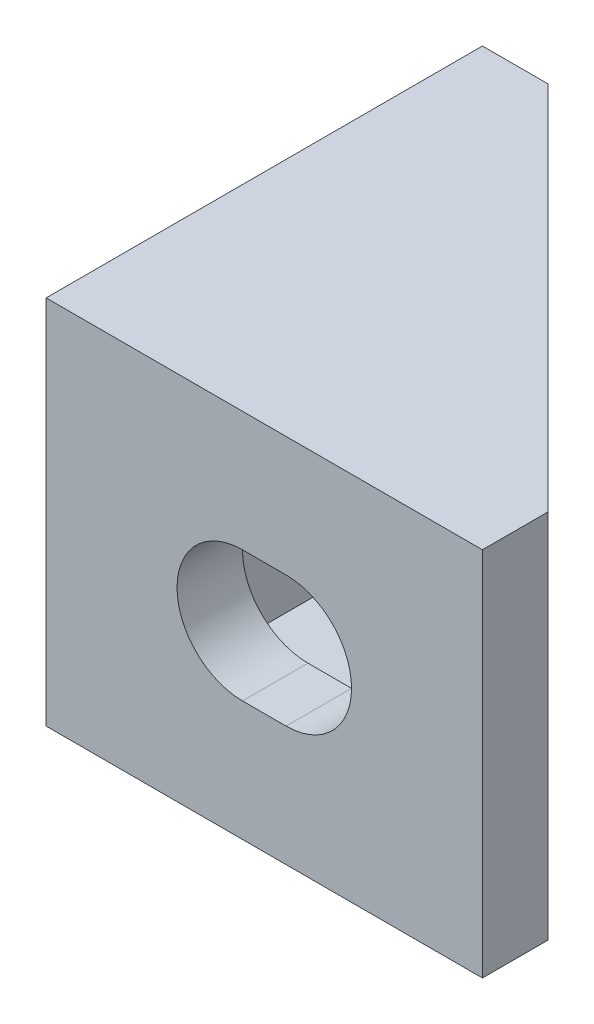
SolidWorks part; units mm, degrees
ref_plane "Front Plane" through (0, 0, 0) normal (0, 0, 1) x (1, 0, 0)
ref_plane "Top Plane" through (0, 0, 0) normal (0, 1, 0) x (1, 0, 0)
ref_plane "Right Plane" through (0, 0, 0) normal (1, 0, 0) x (0, 0, -1)
sketch "Sketch1" plane through (0, 0, 0) normal (0, 1, 0) x (1, 0, 0)
  line L0 (0, 0) -> (20, 0)
  line L1 (20, 0) -> (20, 3)
  line L2 (20, 3) -> (3, 20)
  line L3 (3, 20) -> (0, 20)
  line L4 (0, 20) -> (0, 0)
  dimension "D1" = 20
  dimension "D2" = 20
  dimension "D3" = 3
  dimension "D4" = 3
extrude "Boss-Extrude1" add sketch "Sketch1" along normal blind 17
sketch "Sketch2" plane through (0, 0, -20) normal (0, 0, -1) x (-1, 0, 0)
  line L0 (-3, 15) -> (-20, 15)
  line L1 (-3, 17) -> (-3, 0) construction
  line L2 (-20, 17) -> (-20, 0) construction
  line L3 (-20, 15) -> (-20, 2)
  line L4 (-20, 2) -> (-3, 2)
  line L5 (-3, 2) -> (-3, 15)
  line L6 (-20, 17) -> (-3, 17) construction
  line L7 (-20, 0) -> (-3, 0) construction
  dimension "D1" = 2
  dimension "D2" = 2
extrude "Cut-Extrude1" cut sketch "Sketch2" against normal blind 17
sketch "Sketch3" plane through (3, 0, 0) normal (1, 0, 0) x (0, 0, -1)
  line L0 (9, 8.5) -> (11, 8.5) construction
  line L1 (9, 11.5) -> (11, 11.5)
  line L2 (9, 5.5) -> (11, 5.5)
  line L4 (20, 2) -> (20, 15) construction
  line L5 (0, 17) -> (0, 0) construction
  arc A0 (9, 11.5) -> (9, 5.5) centre (9, 8.5) ccw
  arc A1 (11, 5.5) -> (11, 11.5) centre (11, 8.5) ccw
  point P2 (10, 8.5)
  point P9 (20, 8.5)
  dimension "D2" = 3
  dimension "D1" = 2
  dimension "D3" = 9
extrude "Cut-Extrude2" cut sketch "Sketch3" against normal up to next
sketch "Sketch4" plane through (0, 0, -3) normal (0, 0, -1) x (-1, 0, 0)
  line L0 (-11, 8.5) -> (-9, 8.5) construction
  line L1 (-11, 11.5) -> (-9, 11.5)
  line L2 (-11, 5.5) -> (-9, 5.5)
  line L3 (0, 17) -> (0, 0) construction
  line L4 (-20, 15) -> (-20, 2) construction
  arc A0 (-11, 11.5) -> (-11, 5.5) centre (-11, 8.5) ccw
  arc A1 (-9, 5.5) -> (-9, 11.5) centre (-9, 8.5) ccw
  point P2 (-10, 8.5)
  point P11 (-20, 8.5)
  dimension "D2" = 3
  dimension "D1" = 2
  dimension "D3" = 9
extrude "Cut-Extrude3" cut sketch "Sketch4" against normal up to next
